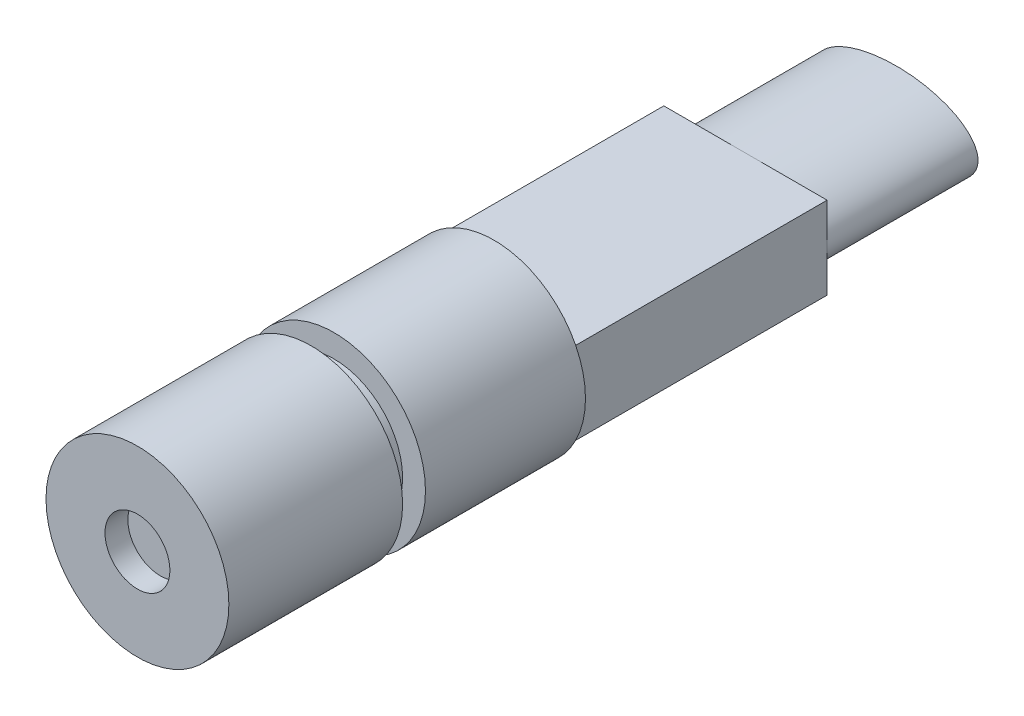
SolidWorks part; units mm, degrees
ref_plane "前视基准面" through (0, 0, 0) normal (0, 0, 1) x (1, 0, 0)
ref_plane "上视基准面" through (0, 0, 0) normal (0, 1, 0) x (1, 0, 0)
ref_plane "右视基准面" through (0, 0, 0) normal (1, 0, 0) x (0, 0, -1)
other "Configuration Table"
sketch "草图1" plane through (0, 0, 0) normal (0, 0, 1) x (1, 0, 0)
  circle A0 centre (0, 0) radius 2
  dimension "D1" = 4
extrude "凸台-拉伸1" add sketch "草图1" along normal blind 7.8
sketch "草图2" plane through (0, 0, 0) normal (0, 0, 1) x (1, 0, 0)
  circle A0 centre (0, 0) radius 2 construction
  circle A1 centre (0, 0) radius 2
  circle A2 centre (0, 0) radius 1.5
  dimension "D1" = 0.5
extrude "切除-拉伸1" cut sketch "草图2" along normal blind 0.5 from offset 3.5
sketch "草图3" plane through (0, 0, 7.8) normal (0, 0, 1) x (1, 0, 0)
  circle A0 centre (0, 0) radius 0.71
  dimension "D1" = 1.42
extrude "切除-拉伸2" cut sketch "草图3" against normal blind 0.5
sketch "草图4" plane through (0, 0, 0) normal (0, 0, 1) x (1, 0, 0)
  line L1 (-1.7861, 0.9) -> (1.7861, 0.9)
  line L2 (-1.7861, 0.9) -> (-1.7861, -0.9)
  line L3 (-1.7861, -0.9) -> (1.7861, -0.9)
  line L4 (1.7861, 0.9) -> (1.7861, -0.9)
  line L5 (-1.7861, 0.9) -> (1.7861, -0.9) construction
  line L6 (-1.7861, -0.9) -> (1.7861, 0.9) construction
  circle A0 centre (0, 0) radius 2 construction
  point P0 (0, 0)
  dimension "D1" = 1.8
extrude "凸台-拉伸2" add sketch "草图4" against normal blind 5.5
sketch "草图5" plane through (0, 0, -5.5) normal (0, 0, -1) x (-1, 0, 0)
  line L0 (1.7861, -0.9) -> (-1.7861, -0.9) construction
  line L1 (-1.7861, -0.9) -> (-1.7861, 0.9) construction
  ellipse E0 centre (0, 0) end of major axis (1.7861, 0) minor radius 0.9
  point P1 (-1.7861, 0)
extrude "凸台-拉伸3" add sketch "草图5" along normal blind 3.3
